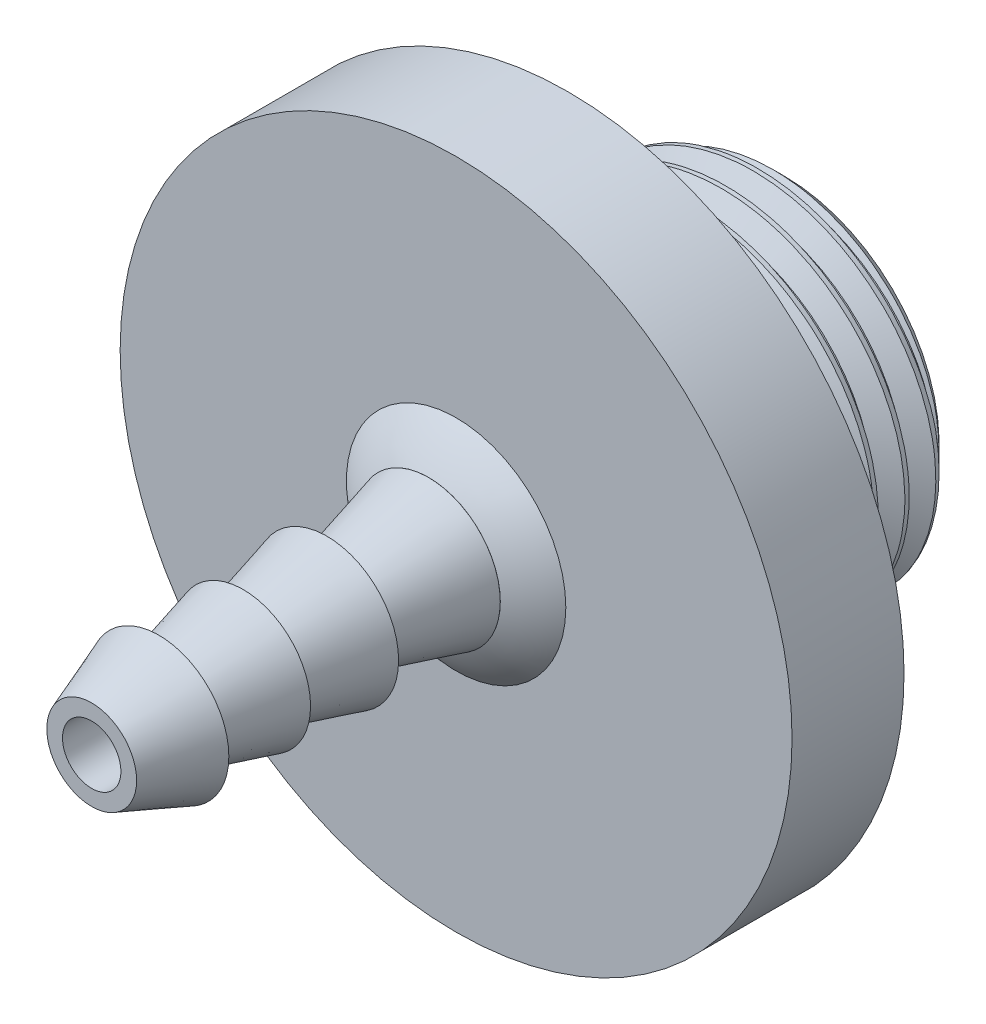
SolidWorks part; units mm, degrees
material "Brass"
ref_plane "Front Plane" through (0, 0, 0) normal (0, 0, 1) x (1, 0, 0)
ref_plane "Top Plane" through (0, 0, 0) normal (0, 1, 0) x (1, 0, 0)
ref_plane "Right Plane" through (0, 0, 0) normal (1, 0, 0) x (0, 0, -1)
sketch "Sketch1" plane through (0, 0, 0) normal (1, 0, 0) x (0, 0, -1)
  line L0 (16.9037, 0) -> (-16.9037, 0) construction
  line L1 (-16.9037, -8.7249) -> (-16.9037, 8.7249) construction
  line L2 (-7.4473, -11.1125) -> (-7.4473, 11.1125) construction
  line L3 (3.1394, -3.2004) -> (3.1394, 3.2004) construction
  line L4 (-0.4623, -10.668) -> (-0.4623, 10.668) construction
  line L5 (-0.4623, 10.668) -> (16.9037, 10.1273) construction
  line L6 (-0.4623, 10.668) -> (1.352, 10.668) construction
  point P0 (-16.9037, -4.7625)
  point P3 (-0.4623, 0)
  point P4 (0, 0)
  point P8 (-16.9037, 0)
  point P9 (-16.9037, 4.7625)
  point P10 (-16.9037, -7.9375)
  point P11 (-16.9037, 7.9375)
  point P16 (-7.4473, 0)
  point P19 (16.9037, 0)
  point P22 (3.1394, 0)
  point P24 (-0.4623, 0)
  dimension "Length" = 33.8074
  dimension "OD2" = 17.4498
  dimension "Tube OD" = 9.525
  dimension "OD1" = 15.875
  dimension "Hex Distance" = 9.4564
  dimension "Hex Size" = 22.225
  dimension "Flow" = 6.4008
  dimension "Insertion" = 20.0431
  dimension "Thread OD" = 21.336
  dimension "Pitch" = 1.8143
  dimension "Hex Length" = 6.985
  dimension "D1" = 1.783
sketch "Sketch2" plane through (0, 0, 0) normal (1, 0, 0) x (0, 0, -1)
  line L0 (-16.9037, 5.2387) -> (-16.9037, 7.5406)
  line L1 (-16.5068, 7.9375) -> (-13.7287, 7.9375)
  line L2 (-13.7287, 7.9375) -> (-13.7287, 7.62)
  line L3 (-13.7287, 7.62) -> (-13.0937, 7.62)
  line L4 (-13.0937, 7.62) -> (-13.0937, 8.2887)
  line L5 (-12.6575, 8.7249) -> (-7.6654, 8.7249)
  line L6 (-7.4473, -11.1125) -> (-7.4473, 11.1125) construction
  line L7 (-7.4473, 8.943) -> (-7.4473, 11.1125)
  line L8 (-7.4473, 11.1125) -> (-0.4623, 11.1125)
  line L13 (3.1394, 3.2004) -> (3.1394, 4.7625)
  line L14 (3.1394, 4.7625) -> (-16.4275, 4.7625)
  line L16 (-16.9037, 5.2387) -> (-16.4275, 4.7625)
  line L22 (-0.4623, 11.1125) -> (-0.4623, 10.668)
  line L23 (-0.4623, 10.668) -> (16.9037, 10.1273)
  line L24 (16.9037, 10.1273) -> (16.9037, 3.2004)
  line L25 (16.9037, 3.2004) -> (3.1394, 3.2004)
  arc A0 (-16.5068, 7.9375) -> (-16.9037, 7.5406) centre (-16.5068, 7.5406) ccw
  arc A1 (-7.4473, 8.943) -> (-7.6654, 8.7249) centre (-7.6654, 8.943) cw
  arc A4 (-12.6575, 8.7249) -> (-13.0937, 8.2887) centre (-12.6575, 8.2887) ccw
  point P28 (-16.9037, 7.9375)
  point P32 (-7.4473, 8.7249)
  dimension "D6" = 0.3969
  dimension "D5" = 0.2181
  dimension "D4" = 0.4362
  dimension "D1" = 3.175
  dimension "D2" = 0.635
  dimension "D3" = 0.3175
  dimension "D7" = 0.4763
  dimension "D8" = 45
revolve "Revolve1" add sketch "Sketch2" angle 360 about L0
sketch "Sketch3" plane through (0, 0, 7.4473) normal (0, 0, 1) x (1, 0, 0)
  line L0 (0, -8.7249) -> (0, 8.7249) construction
  line L1 (0, 12.8316) -> (-11.1125, 6.4158)
  line L2 (-11.1125, 6.4158) -> (-11.1125, -6.4158)
  line L3 (-11.1125, -6.4158) -> (0, -12.8316)
  line L4 (0, -12.8316) -> (11.1125, -6.4158)
  line L5 (11.1125, -6.4158) -> (11.1125, 6.4158)
  line L6 (11.1125, 6.4158) -> (0, 12.8316)
  circle A0 centre (0, 0) radius 11.1125 construction
  circle A1 centre (0, 0) radius 11.1125 construction
  circle A2 centre (0, 0) radius 4.7625
extrude "Boss-Extrude1" add sketch "Sketch3" against normal up to vertex (6.985 mm away) up to point (0, 0, 0.4623)
sketch "Sketch4" plane through (0, 0, 7.4473) normal (0, 0, 1) x (1, 0, 0)
  circle A0 centre (0, 0) radius 11.1125 construction
  circle A1 centre (0, 0) radius 11.1125
extrude "Cut-Extrude1" cut sketch "Sketch4" against normal through all draft 60 flip side to cut
sketch "Sketch9" plane through (0, 0, 0) normal (1, 0, 0) x (0, 0, -1)
  line L0 (3.1394, -4.7625) -> (-16.4275, -4.7625)
  line L1 (-16.4275, 4.7625) -> (3.1394, 4.7625)
  line L2 (-16.4275, 4.7625) -> (3.1394, 4.7625)
  line L3 (3.1394, -4.7625) -> (-16.4275, -4.7625)
  line L4 (-16.9037, 5.2387) -> (-16.4275, 4.7625)
  line L5 (-16.4275, -4.7625) -> (-16.9037, -5.2388)
  line L6 (-16.4275, -4.7625) -> (-16.9037, -5.2388)
  line L7 (-16.9037, 5.2387) -> (-16.4275, 4.7625)
  line L8 (16.9037, -3.2004) -> (3.1394, -3.2004)
  line L9 (3.1394, 3.2004) -> (16.9037, 3.2004)
  line L12 (3.1394, 4.7625) -> (3.1394, 3.2004)
  line L13 (3.1394, -3.2004) -> (3.1394, -4.7625)
  line L14 (16.9037, 0) -> (16.9037, -10.1273) construction
  line L16 (16.9037, -10.1273) -> (12.368, -10.2685) construction
  line L17 (3.1394, 3.2004) -> (16.9037, 3.2004)
  line L18 (16.9037, -3.2004) -> (3.1394, -3.2004)
  line L19 (-0.4623, -10.668) -> (16.9037, -10.1273) construction
  arc A0 (-7.4473, -8.943) -> (-7.6654, -8.7249) centre (-7.6654, -8.943) ccw
  arc A1 (-7.6654, 8.7249) -> (-7.4473, 8.943) centre (-7.6654, 8.943) ccw
  arc A2 (-7.6654, 8.7249) -> (-7.4473, 8.943) centre (-7.6654, 8.943) ccw
  arc A3 (-7.4473, -8.943) -> (-7.6654, -8.7249) centre (-7.6654, -8.943) ccw
  dimension "D1" = 4.5357
fillet "Fillet1" radius 2.7781 6 edges at (11.1125, -6.4158, 3.4585) (0, -12.8316, 3.4585) (-11.1125, -6.4158, 3.4585) (-11.1125, 6.4158, 3.4585) (0, 12.8316, 3.4585) (11.1125, 6.4158, 3.4585)
sketch "Sketch8" plane through (0, 0, 0) normal (1, 0, 0) x (0, 0, -1)
  line L0 (-0.4623, -16.6687) -> (-0.4623, 16.6687)
  line L1 (0, 0) -> (10.9786, 0) construction
  line L2 (16.9037, 0) -> (-16.9037, 0) construction
  line L4 (-0.4623, -10.668) -> (-0.4623, 10.668) construction
  point P5 (16.9037, 0)
  dimension "D1" = 33.3375
split "Split1" trim tools "Sketch8" bodies to split 106 113 resulting bodies 109 110
sketch "Sketch6" plane through (0, 0, -16.9037) normal (0, 0, -1) x (-1, 0, 0)
  circle A0 centre (0, 0) radius 10.1273 construction
  circle A4 centre (0, 0) radius 10.1273
curve "Helix/Spiral1"
sketch "Sketch7" plane through (0, 0, 0) normal (1, 0, 0) x (0, 0, -1)
  line L0 (16.7903, 10.3237) -> (18.6046, 10.3237) construction
  line L1 (18.6046, 10.3237) -> (17.6974, 8.7525) construction
  line L2 (17.6974, 8.7525) -> (16.7903, 10.3237) construction
  line L3 (17.6974, 10.3237) -> (17.6974, 10.1273) construction
  line L4 (17.6974, 10.1273) -> (17.6974, 8.9489) construction
  line L5 (17.6974, 8.9489) -> (17.6974, 8.7525) construction
  line L6 (16.9037, 10.1273) -> (18.4912, 10.1273) construction
  line L7 (17.5841, 8.9489) -> (17.8108, 8.9489)
  line L8 (16.847, 10.2255) -> (18.5479, 10.2255)
  line L9 (16.847, 10.2255) -> (17.5841, 8.9489)
  line L10 (18.5479, 10.2255) -> (17.8108, 8.9489)
  line L11 (-0.4623, 10.668) -> (16.9037, 10.1273) construction
  point P10 (17.6974, 10.1273)
  point P13 (17.6974, 8.9489)
  point P16 (17.6974, 10.2255)
  dimension "D1" = 1.8143
  dimension "D2" = 0.2268
sweep "Cut-Sweep1" cut profiles "Sketch7" path "Helix/Spiral1"
sketch "Sketch5" plane through (0, 0, -16.9037) normal (0, 0, -1) x (-1, 0, 0)
  circle A0 centre (0, 0) radius 8.7525
extrude "Cut-Extrude2" cut sketch "Sketch5" against normal through all draft 45 flip side to cut
combine bodies "Combine1" operation type add bodies to combine 110 111
chamfer "Chamfer1" distance 0.508 angle 45 1 edges at (0, 3.2004, -16.9037)
sketch "Sketch10" plane through (0, 0, 0.4623) normal (0, 0, -1) x (-1, 0, 0)
  line L6 (-11.1125, 4.8119) -> (-11.1125, -4.8119)
  line L7 (-9.7234, -7.2178) -> (-1.3891, -12.0296)
  line L8 (1.3891, -12.0296) -> (9.7234, -7.2178)
  line L9 (11.1125, -4.8119) -> (11.1125, 4.8119)
  line L10 (9.7234, 7.2178) -> (1.3891, 12.0296)
  line L11 (-1.3891, 12.0296) -> (-9.7234, 7.2178)
  line L12 (-11.1125, 4.8119) -> (-11.1125, -4.8119)
  line L13 (-9.7234, -7.2178) -> (-1.3891, -12.0296)
  line L14 (1.3891, -12.0296) -> (9.7234, -7.2178)
  line L15 (11.1125, -4.8119) -> (11.1125, 4.8119)
  line L16 (9.7234, 7.2178) -> (1.3891, 12.0296)
  line L17 (-1.3891, 12.0296) -> (-9.7234, 7.2178)
  arc A6 (-11.1125, -4.8119) -> (-9.7234, -7.2178) centre (-8.3344, -4.8119) ccw
  arc A7 (-1.3891, -12.0296) -> (1.3891, -12.0296) centre (0, -9.6237) ccw
  arc A8 (9.7234, -7.2178) -> (11.1125, -4.8119) centre (8.3344, -4.8119) ccw
  arc A9 (11.1125, 4.8119) -> (9.7234, 7.2178) centre (8.3344, 4.8119) ccw
  arc A10 (1.3891, 12.0296) -> (-1.3891, 12.0296) centre (0, 9.6237) ccw
  arc A11 (-9.7234, 7.2178) -> (-11.1125, 4.8119) centre (-8.3344, 4.8119) ccw
  arc A12 (-11.1125, -4.8119) -> (-9.7234, -7.2178) centre (-8.3344, -4.8119) ccw
  arc A13 (-1.3891, -12.0296) -> (1.3891, -12.0296) centre (0, -9.6237) ccw
  arc A14 (9.7234, -7.2178) -> (11.1125, -4.8119) centre (8.3344, -4.8119) ccw
  arc A15 (11.1125, 4.8119) -> (9.7234, 7.2178) centre (8.3344, 4.8119) ccw
  arc A16 (1.3891, 12.0296) -> (-1.3891, 12.0296) centre (0, 9.6237) ccw
  arc A17 (-9.7234, 7.2178) -> (-11.1125, 4.8119) centre (-8.3344, 4.8119) ccw
  dimension "D1" = 0
extrude "Cut-Extrude3" cut sketch "Sketch10" against normal through all
sketch "Sketch11" plane through (0, 0, -16.9037) normal (0, 0, -1) x (-1, 0, 0)
  circle A0 centre (0, 0) radius 6.35
  dimension "D1" = 12.7
extrude "Cut-Extrude4" cut sketch "Sketch11" against normal through all
sketch "Sketch16" plane through (0, 0, 0.4623) normal (0, 0, 1) x (1, 0, 0)
  circle A0 centre (0, 0) radius 12.7
  dimension "D1" = 25.4
extrude "Cut-Extrude8" cut sketch "Sketch16" against normal blind 5.08
sketch "Sketch18" plane through (0, 0, 0) normal (0, 1, 0) x (1, 0, 0)
  line L0 (-6.35, 4.6177) -> (6.35, 4.6177) construction
  line L2 (2.5456, -22.3956) -> (1.6566, -22.3956)
  line L3 (3.9669, -18.5856) -> (2.5456, -18.5856)
  line L4 (3.8156, -13.8007) -> (2.8037, -13.8007)
  line L5 (2.5456, -22.3956) -> (3.9669, -18.5856)
  line L6 (4.064, -9.0572) -> (2.5346, -9.0572)
  line L7 (6.35, 4.6177) -> (8.89, 4.6177)
  line L8 (4.064, -3.295) -> (4.064, -3.289)
  line L9 (1.6566, -1.5124) -> (1.6566, -4.2309)
  line L10 (3.8156, -13.8007) -> (2.5456, -18.5856)
  line L11 (4.064, -9.0572) -> (2.8037, -13.8007)
  line L12 (4.064, -3.295) -> (2.5346, -9.0572)
  line L13 (1.6566, -4.2309) -> (1.6566, -22.3956)
  line L14 (0, 1.4427) -> (0, 4.6177) construction
  line L16 (6.2217, -1.7323) -> (19.05, -1.7323)
  line L18 (6.35, 4.6177) -> (19.05, 4.6177)
  line L19 (19.05, -1.7323) -> (19.05, 4.6177)
  arc A0 (1.6566, -1.5124) -> (6.35, 4.6177) centre (0, 4.6177) ccw
  arc A1 (4.064, -3.289) -> (6.2217, -1.7323) centre (0, 4.6177) ccw
  circle A2 centre (0, 4.6177) radius 8.89 construction
  circle A3 centre (0, 4.6177) radius 6.35 construction
  point P9 (0, 4.6177)
  point P30 (0, 1.4427)
  dimension "D2" = 6.35
revolve "Revolve2" add sketch "Sketch18" angle 360 about L14
equation "\"D6@Sketch2\"=\"OD1@Sketch1\"*0.025"
equation "\"D7@Sketch2\"=\"Tube OD@Sketch1\"*0.05"
equation "\"D1@Fillet1\"=\"Hex Size@Sketch1\"*0.125"
equation "\"D3@Helix/Spiral1\" = \"Length@Sketch1\" - \"Hex Distance@Sketch1\" - \"Hex Length@Sketch1\" + \"Pitch@Sketch1\""
equation "\"D1@Sketch7\"=\"Pitch@Sketch1\""
equation "\"D2@Sketch7\"=\"D1@Sketch7\"/8"
equation "\"D1@Sketch8\"=\"Hex Size@Sketch1\"*1.5"
equation "\"D4@Helix/Spiral1\"=\"Pitch@Sketch1\""
equation "\"D1@Sketch9\"=\"Pitch@Sketch1\"*2.5"
equation "\"D5@Sketch2\"=\"D4@Sketch2\"*0.5"
equation "\"D1\"= \"Hex Length@Sketch1\" * 0.625"
equation "\"D4@Sketch2\"=\"OD2@Sketch1\"*0.025"
